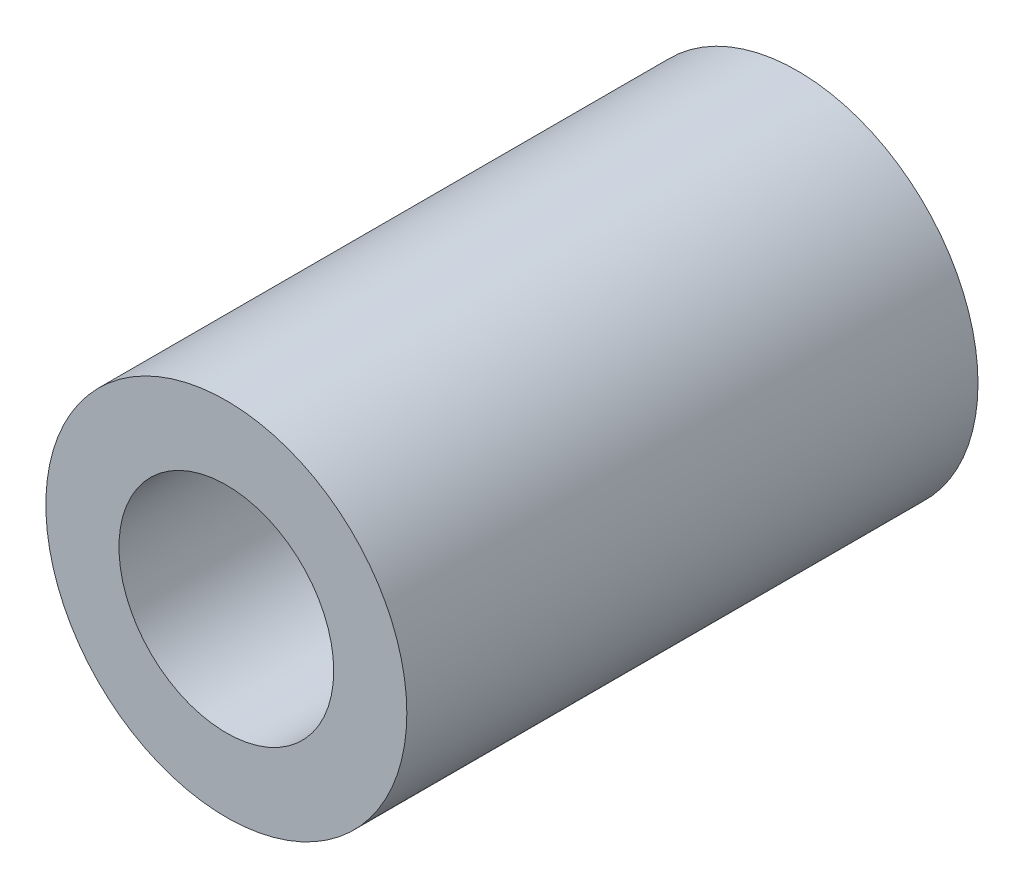
SolidWorks part; units mm, degrees
ref_plane "Front Plane" through (0, 0, 0) normal (0, 0, 1) x (1, 0, 0)
ref_plane "Top Plane" through (0, 0, 0) normal (0, 1, 0) x (1, 0, 0)
ref_plane "Right Plane" through (0, 0, 0) normal (1, 0, 0) x (0, 0, -1)
sketch "Sketch1" plane through (0, 0, 0) normal (0, 0, 1) x (1, 0, 0)
  circle A0 centre (0, 0) radius 7.9
  circle A1 centre (0, 0) radius 4.7
  dimension "D1" = 15.8
  dimension "D2" = 9.4
extrude "Boss-Extrude1" add sketch "Sketch1" against normal blind 25
